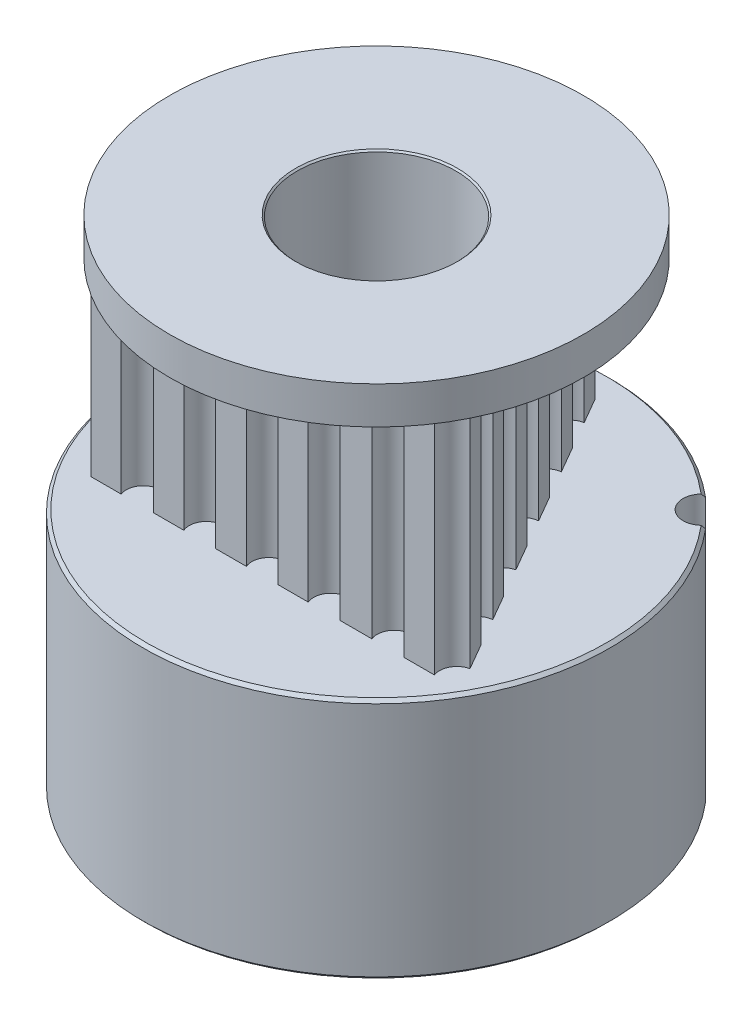
SolidWorks part; units mm, degrees
material "6061 slitina"
ref_plane "Přední rovina" through (0, 0, 0) normal (0, 0, 1) x (1, 0, 0)
ref_plane "Horní rovina" through (0, 0, 0) normal (0, 1, 0) x (1, 0, 0)
ref_plane "Pravá rovina" through (0, 0, 0) normal (1, 0, 0) x (0, 0, -1)
sketch "Skica1" plane through (0, 0, 0) normal (0, 1, 0) x (1, 0, 0)
  circle A0 centre (0, 0) radius 2.5
  arc B0 (-5.7301, 1.0983) -> (-5.3872, 2.2403) centre (-5.6803, 1.7058) ccw
  arc B1 (-5.7301, 1.0983) -> (-5.922, 1.0859) centre (-5.7841, 0.4401) ccw
  arc B2 (-5.922, 1.0859) -> (-6.0197, 1.0387) centre (-5.8743, 0.8624) ccw
  arc B3 (-6.0197, 1.0387) -> (-6.0791, 0.6004) centre (0, 0) ccw
  arc B4 (-6.0791, 0.6004) -> (-5.9974, 0.5289) centre (-5.892, 0.7317) ccw
  arc B5 (-5.9974, 0.5289) -> (-5.8158, 0.466) centre (-5.6927, 1.1148) ccw
  arc B6 (-5.7891, -0.7262) -> (-5.8158, 0.466) centre (-5.9294, -0.133) ccw
  arc B7 (-5.7891, -0.7262) -> (-5.9677, -0.7972) centre (-5.637, -1.3689) ccw
  arc B8 (-5.9677, -0.7972) -> (-6.0461, -0.8723) centre (-5.8532, -0.9951) ccw
  arc B9 (-6.0461, -0.8723) -> (-5.9671, -1.3075) centre (0, 0) ccw
  arc B10 (-5.9671, -1.3075) -> (-5.8673, -1.3503) centre (-5.8297, -1.1248) ccw
  arc B11 (-5.8673, -1.3503) -> (-5.6751, -1.354) centre (-5.7586, -0.6989) ccw
  arc B12 (-5.2813, -2.4796) -> (-5.6751, -1.354) centre (-5.5981, -1.9587) ccw
  arc B13 (-5.2813, -2.4796) -> (-5.4293, -2.6023) centre (-4.9381, -3.0438) ccw
  arc B14 (-5.4293, -2.6023) -> (-5.4806, -2.698) centre (-5.2593, -2.7551) ccw
  arc B15 (-5.4806, -2.698) -> (-5.271, -3.0875) centre (0, 0) ccw
  arc B16 (-5.271, -3.0875) -> (-5.1629, -3.0973) centre (-5.1968, -2.8713) ccw
  arc B17 (-5.1629, -3.0973) -> (-4.979, -3.0415) centre (-5.2608, -2.4442) ccw
  arc B18 (-4.2566, -3.9902) -> (-4.979, -3.0415) centre (-4.7188, -3.5928) ccw
  arc B19 (-4.2566, -3.9902) -> (-4.3594, -4.1527) centre (-3.7559, -4.4208) ccw
  arc B20 (-4.3594, -4.1527) -> (-4.3786, -4.2595) centre (-4.1505, -4.2455) ccw
  arc B21 (-4.3786, -4.2595) -> (-4.059, -4.5652) centre (0, 0) ccw
  arc B22 (-4.059, -4.5652) -> (-3.9531, -4.5412) centre (-4.0552, -4.3366) ccw
  arc B23 (-3.9531, -4.5412) -> (-3.7954, -4.4312) centre (-4.248, -3.9503) ccw
  arc B24 (-2.8152, -5.1103) -> (-3.7954, -4.4312) centre (-3.3776, -4.8751) ccw
  arc B25 (-2.8152, -5.1103) -> (-2.8628, -5.2965) centre (-2.2059, -5.3651) ccw
  arc B26 (-2.8628, -5.2965) -> (-2.8481, -5.4041) centre (-2.6354, -5.3203) ccw
  arc B27 (-2.8481, -5.4041) -> (-2.4496, -5.596) centre (0, 0) ccw
  arc B28 (-2.4496, -5.596) -> (-2.3563, -5.5405) centre (-2.5166, -5.3775) ccw
  arc B29 (-2.3563, -5.5405) -> (-2.2403, -5.3872) centre (-2.8194, -5.0696) ccw
  arc B30 (-1.0983, -5.7301) -> (-2.2403, -5.3872) centre (-1.7058, -5.6803) ccw
  arc B31 (-1.0983, -5.7301) -> (-1.0859, -5.922) centre (-0.4401, -5.7841) ccw
  arc B32 (-1.0859, -5.922) -> (-1.0387, -6.0197) centre (-0.8624, -5.8743) ccw
  arc B33 (-1.0387, -6.0197) -> (-0.6004, -6.0791) centre (0, 0) ccw
  arc B34 (-0.6004, -6.0791) -> (-0.5289, -5.9974) centre (-0.7317, -5.892) ccw
  arc B35 (-0.5289, -5.9974) -> (-0.466, -5.8158) centre (-1.1148, -5.6927) ccw
  arc B36 (0.7262, -5.7891) -> (-0.466, -5.8158) centre (0.133, -5.9294) ccw
  arc B37 (0.7262, -5.7891) -> (0.7972, -5.9677) centre (1.3689, -5.637) ccw
  arc B38 (0.7972, -5.9677) -> (0.8723, -6.0461) centre (0.9951, -5.8532) ccw
  arc B39 (0.8723, -6.0461) -> (1.3075, -5.9671) centre (0, 0) ccw
  arc B40 (1.3075, -5.9671) -> (1.3503, -5.8673) centre (1.1248, -5.8297) ccw
  arc B41 (1.3503, -5.8673) -> (1.354, -5.6751) centre (0.6989, -5.7586) ccw
  arc B42 (2.4796, -5.2813) -> (1.354, -5.6751) centre (1.9587, -5.5981) ccw
  arc B43 (2.4796, -5.2813) -> (2.6023, -5.4293) centre (3.0438, -4.9381) ccw
  arc B44 (2.6023, -5.4293) -> (2.698, -5.4806) centre (2.7551, -5.2593) ccw
  arc B45 (2.698, -5.4806) -> (3.0875, -5.271) centre (0, 0) ccw
  arc B46 (3.0875, -5.271) -> (3.0973, -5.1629) centre (2.8713, -5.1968) ccw
  arc B47 (3.0973, -5.1629) -> (3.0415, -4.979) centre (2.4442, -5.2608) ccw
  arc B48 (3.9902, -4.2566) -> (3.0415, -4.979) centre (3.5928, -4.7188) ccw
  arc B49 (3.9902, -4.2566) -> (4.1527, -4.3594) centre (4.4208, -3.7559) ccw
  arc B50 (4.1527, -4.3594) -> (4.2595, -4.3786) centre (4.2455, -4.1505) ccw
  arc B51 (4.2595, -4.3786) -> (4.5652, -4.059) centre (0, 0) ccw
  arc B52 (4.5652, -4.059) -> (4.5412, -3.9531) centre (4.3366, -4.0552) ccw
  arc B53 (4.5412, -3.9531) -> (4.4312, -3.7954) centre (3.9503, -4.248) ccw
  arc B54 (5.1103, -2.8152) -> (4.4312, -3.7954) centre (4.8751, -3.3776) ccw
  arc B55 (5.1103, -2.8152) -> (5.2965, -2.8628) centre (5.3651, -2.2059) ccw
  arc B56 (5.2965, -2.8628) -> (5.4041, -2.8481) centre (5.3203, -2.6354) ccw
  arc B57 (5.4041, -2.8481) -> (5.596, -2.4496) centre (0, 0) ccw
  arc B58 (5.596, -2.4496) -> (5.5405, -2.3563) centre (5.3775, -2.5166) ccw
  arc B59 (5.5405, -2.3563) -> (5.3872, -2.2403) centre (5.0696, -2.8194) ccw
  arc B60 (5.7301, -1.0983) -> (5.3872, -2.2403) centre (5.6803, -1.7058) ccw
  arc B61 (5.7301, -1.0983) -> (5.922, -1.0859) centre (5.7841, -0.4401) ccw
  arc B62 (5.922, -1.0859) -> (6.0197, -1.0387) centre (5.8743, -0.8624) ccw
  arc B63 (6.0197, -1.0387) -> (6.0791, -0.6004) centre (0, 0) ccw
  arc B64 (6.0791, -0.6004) -> (5.9974, -0.5289) centre (5.892, -0.7317) ccw
  arc B65 (5.9974, -0.5289) -> (5.8158, -0.466) centre (5.6927, -1.1148) ccw
  arc B66 (5.7891, 0.7262) -> (5.8158, -0.466) centre (5.9294, 0.133) ccw
  arc B67 (5.7891, 0.7262) -> (5.9677, 0.7972) centre (5.637, 1.3689) ccw
  arc B68 (5.9677, 0.7972) -> (6.0461, 0.8723) centre (5.8532, 0.9951) ccw
  arc B69 (6.0461, 0.8723) -> (5.9671, 1.3075) centre (0, 0) ccw
  arc B70 (5.9671, 1.3075) -> (5.8673, 1.3503) centre (5.8297, 1.1248) ccw
  arc B71 (5.8673, 1.3503) -> (5.6751, 1.354) centre (5.7586, 0.6989) ccw
  arc B72 (5.2813, 2.4796) -> (5.6751, 1.354) centre (5.5981, 1.9587) ccw
  arc B73 (5.2813, 2.4796) -> (5.4293, 2.6023) centre (4.9381, 3.0438) ccw
  arc B74 (5.4293, 2.6023) -> (5.4806, 2.698) centre (5.2593, 2.7551) ccw
  arc B75 (5.4806, 2.698) -> (5.271, 3.0875) centre (0, 0) ccw
  arc B76 (5.271, 3.0875) -> (5.1629, 3.0973) centre (5.1968, 2.8713) ccw
  arc B77 (5.1629, 3.0973) -> (4.979, 3.0415) centre (5.2608, 2.4442) ccw
  arc B78 (4.2566, 3.9902) -> (4.979, 3.0415) centre (4.7188, 3.5928) ccw
  arc B79 (4.2566, 3.9902) -> (4.3594, 4.1527) centre (3.7559, 4.4208) ccw
  arc B80 (4.3594, 4.1527) -> (4.3786, 4.2595) centre (4.1505, 4.2455) ccw
  arc B81 (4.3786, 4.2595) -> (4.059, 4.5652) centre (0, 0) ccw
  arc B82 (4.059, 4.5652) -> (3.9531, 4.5412) centre (4.0552, 4.3366) ccw
  arc B83 (3.9531, 4.5412) -> (3.7954, 4.4312) centre (4.248, 3.9503) ccw
  arc B84 (2.8152, 5.1103) -> (3.7954, 4.4312) centre (3.3776, 4.8751) ccw
  arc B85 (2.8152, 5.1103) -> (2.8628, 5.2965) centre (2.2059, 5.3651) ccw
  arc B86 (2.8628, 5.2965) -> (2.8481, 5.4041) centre (2.6354, 5.3203) ccw
  arc B87 (2.8481, 5.4041) -> (2.4496, 5.596) centre (0, 0) ccw
  arc B88 (2.4496, 5.596) -> (2.3563, 5.5405) centre (2.5166, 5.3775) ccw
  arc B89 (2.3563, 5.5405) -> (2.2403, 5.3872) centre (2.8194, 5.0696) ccw
  arc B90 (1.0983, 5.7301) -> (2.2403, 5.3872) centre (1.7058, 5.6803) ccw
  arc B91 (1.0983, 5.7301) -> (1.0859, 5.922) centre (0.4401, 5.7841) ccw
  arc B92 (1.0859, 5.922) -> (1.0387, 6.0197) centre (0.8624, 5.8743) ccw
  arc B93 (1.0387, 6.0197) -> (0.6004, 6.0791) centre (0, 0) ccw
  arc B94 (0.6004, 6.0791) -> (0.5289, 5.9974) centre (0.7317, 5.892) ccw
  arc B95 (0.5289, 5.9974) -> (0.466, 5.8158) centre (1.1148, 5.6927) ccw
  arc B96 (-0.7262, 5.7891) -> (0.466, 5.8158) centre (-0.133, 5.9294) ccw
  arc B97 (-0.7262, 5.7891) -> (-0.7972, 5.9677) centre (-1.3689, 5.637) ccw
  arc B98 (-0.7972, 5.9677) -> (-0.8723, 6.0461) centre (-0.9951, 5.8532) ccw
  arc B99 (-0.8723, 6.0461) -> (-1.3075, 5.9671) centre (0, 0) ccw
  arc B100 (-1.3075, 5.9671) -> (-1.3503, 5.8673) centre (-1.1248, 5.8297) ccw
  arc B101 (-1.3503, 5.8673) -> (-1.354, 5.6751) centre (-0.6989, 5.7586) ccw
  arc B102 (-2.4796, 5.2813) -> (-1.354, 5.6751) centre (-1.9587, 5.5981) ccw
  arc B103 (-2.4796, 5.2813) -> (-2.6023, 5.4293) centre (-3.0438, 4.9381) ccw
  arc B104 (-2.6023, 5.4293) -> (-2.698, 5.4806) centre (-2.7551, 5.2593) ccw
  arc B105 (-2.698, 5.4806) -> (-3.0875, 5.271) centre (0, 0) ccw
  arc B106 (-3.0875, 5.271) -> (-3.0973, 5.1629) centre (-2.8713, 5.1968) ccw
  arc B107 (-3.0973, 5.1629) -> (-3.0415, 4.979) centre (-2.4442, 5.2608) ccw
  arc B108 (-3.9902, 4.2566) -> (-3.0415, 4.979) centre (-3.5928, 4.7188) ccw
  arc B109 (-3.9902, 4.2566) -> (-4.1527, 4.3594) centre (-4.4208, 3.7559) ccw
  arc B110 (-4.1527, 4.3594) -> (-4.2595, 4.3786) centre (-4.2455, 4.1505) ccw
  arc B111 (-4.2595, 4.3786) -> (-4.5652, 4.059) centre (0, 0) ccw
  arc B112 (-4.5652, 4.059) -> (-4.5412, 3.9531) centre (-4.3366, 4.0552) ccw
  arc B113 (-4.5412, 3.9531) -> (-4.4312, 3.7954) centre (-3.9503, 4.248) ccw
  arc B114 (-5.1103, 2.8152) -> (-4.4312, 3.7954) centre (-4.8751, 3.3776) ccw
  arc B115 (-5.1103, 2.8152) -> (-5.2965, 2.8628) centre (-5.3651, 2.2059) ccw
  arc B116 (-5.2965, 2.8628) -> (-5.4041, 2.8481) centre (-5.3203, 2.6354) ccw
  arc B117 (-5.4041, 2.8481) -> (-5.596, 2.4496) centre (0, 0) ccw
  arc B118 (-5.596, 2.4496) -> (-5.5405, 2.3563) centre (-5.3775, 2.5166) ccw
  arc B119 (-5.5405, 2.3563) -> (-5.3872, 2.2403) centre (-5.0696, 2.8194) ccw
  dimension "D1" = 5
sketch_block_instance "Blok1-1"
sketch_block "Blok1"
extrude "Přidat vysunutím1" add sketch "Skica1" along normal blind 7 from offset 7.8
sketch "Skica2" plane through (0, 7.8, 0) normal (0, -1, 0) x (1, 0, 0)
  circle A0 centre (0, 0) radius 3.5
  circle A1 centre (0, 0) radius 2.5 construction
  circle A2 centre (0, 0) radius 2.5
  dimension "D1" = 7
extrude "Přidat vysunutím2" add sketch "Skica2" along normal blind 7.8
sketch "Skica3" plane through (0, 14.8, 0) normal (0, 1, 0) x (1, 0, 0)
  circle A0 centre (0, 0) radius 3.5
  circle A1 centre (0, 0) radius 2.5 construction
  circle A2 centre (0, 0) radius 2.5
  dimension "D1" = 7
extrude "Přidat vysunutím3" add sketch "Skica3" along normal blind 1.2
sketch "Skica5" plane through (0, 16, 0) normal (0, 1, 0) x (1, 0, 0)
  circle A0 centre (0, 0) radius 7.5
  circle A3 centre (0, 0) radius 3.5 construction
  circle A4 centre (0, 0) radius 3.5
  dimension "D1" = 15
extrude "Přidat vysunutím4" add sketch "Skica5" against normal up to surface (1.2 mm away) separate body up to face at (0, 14.8, 0)
sketch "Skica6" plane through (0, 0, 0) normal (0, -1, 0) x (1, 0, 0)
  circle A0 centre (0, 0) radius 7.5
  circle A1 centre (0, 0) radius 3.5 construction
  circle A2 centre (0, 0) radius 3.5
  circle A3 centre (0, 0) radius 7.5 construction
extrude "Přidat vysunutím5" add sketch "Skica6" against normal up to surface (7.8 mm away) separate body up to face at (0, 7.8, 0)
chamfer "Zkosení1" distance 0.1 angle 45 2 edges at (0, 14.8, 7.5) (0, 16, 7.5)
chamfer "Zkosení2" distance 0.1 angle 45 2 edges at (0, 0, -2.5) (0, 16, 2.5)
chamfer "Zkosení3" distance 0.1 angle 45 2 edges at (0, 0, -7.5) (0, 7.8, 7.5)
sketch "Sketch8" plane through (0, 16, 0) normal (0, 1, 0) x (1, 0, 0)
  circle A0 centre (0, 0) radius 6.65
extrude "Cut-Extrude2" cut sketch "Sketch8" against normal blind 5 flip side to cut contours A0
ref_plane "Plane1" through (0, 0, -7.5) normal (0, 0, -1) x (-1, 0, 0)
ref_plane "Plane2" through (-7.5, 0, 0) normal (-1, 0, 0) x (0, 0, 1)
sketch "Sketch20" plane through (-7.5, 0, 0) normal (-1, 0, 0) x (0, 0, 1)
  line L0 (0, 0.1) -> (0, 7.7)
  line L1 (-7.5, 0.1) -> (7.5, 0.1) construction
  line L2 (7.5, 7.7) -> (-7.5, 7.7) construction
  circle A0 centre (0, 3.9) radius 1.5
sketch "Sketch25" plane through (0, 7.8, 0) normal (0, 1, 0) x (1, 0, 0)
  line L0 (-0.7179, 6.0965) -> (-0.9071, 5.7689)
  line L5 (-5.5084, -3.67) -> (-4.5368, -3.67)
  line L6 (5.926, -2.9242) -> (5.4338, -2.0716)
  line L9 (-5.4363, -2.0759) -> (-5.8989, -2.8773)
  line L23 (-3.4987, -3.67) -> (-2.5208, -3.67)
  line L24 (-4.4422, -0.3541) -> (-4.912, -1.1678)
  line L26 (-1.4992, -3.67) -> (-0.513, -3.67)
  line L27 (2.4958, -3.67) -> (3.5189, -3.67)
  line L28 (4.926, -1.192) -> (4.4459, -0.3606)
  line L29 (4.549, -3.67) -> (5.5306, -3.67)
  line L30 (0.5086, -3.67) -> (1.4742, -3.67)
  line L31 (3.9112, 0.5657) -> (3.4185, 1.419)
  line L32 (1.9163, 4.0209) -> (1.4364, 4.8521)
  line L33 (-1.4233, 4.8748) -> (-1.9185, 4.0171)
  line L34 (2.9152, 2.2908) -> (2.4274, 3.1357)
  line L35 (0.9141, 5.7568) -> (0.4321, 6.5916)
  line L37 (-2.4409, 3.1122) -> (-2.9162, 2.2891)
  line L39 (-0.7179, 6.0965) -> (-0.4321, 6.5916)
  line L40 (-3.4352, 1.3901) -> (-3.9277, 0.5371)
  line L42 (-0.4321, 6.5916) -> (-0.9071, 5.7689) [skipped]
  arc A24 (-0.4321, 6.5916) -> (0.4321, 6.5916) centre (0, 6.94) ccw
  arc A25 (-1.4233, 4.8748) -> (-0.9071, 5.7689) centre (-0.9887, 5.22) ccw
  arc A26 (-2.4409, 3.1122) -> (-1.9185, 4.0171) centre (-2.0176, 3.471) ccw
  arc A27 (0.9141, 5.7568) -> (1.4364, 4.8521) centre (1.0128, 5.2106) ccw
  arc A28 (1.9163, 4.0209) -> (2.4274, 3.1357) centre (1.9844, 3.4701) ccw
  arc A29 (-3.4352, 1.3901) -> (-2.9162, 2.2891) centre (-3.0054, 1.7413) ccw
  arc A30 (-4.4422, -0.3541) -> (-3.9277, 0.5371) centre (-4.0048, -0.0125) ccw
  arc A31 (-5.4363, -2.0759) -> (-4.912, -1.1678) centre (-5.0165, -1.7129) ccw
  arc A32 (-5.5084, -3.67) -> (-5.8989, -2.8773) centre (-6.0049, -3.4221) ccw
  arc A33 (-3.4987, -3.67) -> (-4.5368, -3.67) centre (-4.0177, -3.4735) ccw
  arc A34 (-1.4992, -3.67) -> (-2.5208, -3.67) centre (-2.01, -3.4529) ccw
  arc A35 (0.5086, -3.67) -> (-0.513, -3.67) centre (-0.0022, -3.4529) ccw
  arc A36 (2.4958, -3.67) -> (1.4742, -3.67) centre (1.985, -3.4529) ccw
  arc A37 (4.549, -3.67) -> (3.5189, -3.67) centre (4.0339, -3.4632) ccw
  arc A38 (2.9152, 2.2908) -> (3.4185, 1.419) centre (2.9643, 1.738) ccw
  arc A39 (3.9112, 0.5657) -> (4.4459, -0.3606) centre (4.05, 0.0283) ccw
  arc A40 (4.926, -1.192) -> (5.4338, -2.0716) centre (4.9859, -1.7438) ccw
  arc A41 (5.926, -2.9242) -> (5.5306, -3.67) centre (6.0467, -3.4659) ccw
  point P0 (-1.0017, 5.205)
  point P6 (-2.0034, 3.47)
  point P7 (-3.0051, 1.735)
  point P8 (0, 0)
  point P9 (-4.0068, 0)
  point P10 (-5.0085, -1.735)
  point P11 (5.0085, -1.735)
  point P12 (4.0068, 0)
  point P13 (3.0051, 1.735)
  point P14 (2.0034, 3.47)
  point P15 (1.0017, 5.205)
  point P16 (-4.0068, -3.47)
  point P20 (-2.0034, -3.47)
  point P21 (0, -3.47)
  point P23 (2.0034, -3.47)
  point P24 (4.0068, -3.47)
sketch "Sketch30" plane through (0, 0, 0) normal (0, -1, 0) x (1, 0, 0)
  line L0 (0, 0) -> (6.782, 0)
  line L1 (6.782, 0) -> (0, -6.782)
  line L2 (-0.1186, 0) -> (3.391, -3.391)
  line L3 (3.391, -3.391) -> (4.7956, -4.7956)
  line L4 (4.7956, -4.7956) -> (5.2326, -5.2326)
  circle A0 centre (0, 0) radius 6.782
  circle A1 centre (0, 0) radius 7.4 construction
  circle A2 centre (5.2326, -5.2326) radius 0.618
sketch "Sketch31" plane through (0, 0, 0) normal (0, -1, 0) x (1, 0, 0)
  circle A1 centre (0, 0) radius 2.55
sketch "Sketch19" plane through (0, 0, -7.5) normal (0, 0, -1) x (-1, 0, 0)
  line L0 (0, 0.1) -> (0, 7.7)
  line L1 (7.5, 0.1) -> (-7.5, 0.1) construction
  line L2 (-7.5, 7.7) -> (7.5, 7.7) construction
  circle A0 centre (0, 3.9) radius 1.5
sketch "Sketch32" plane through (0, 7.8, 0) normal (0, 1, 0) x (1, 0, 0)
  circle A0 centre (0, 0) radius 6.65
extrude "Cut-Extrude3" cut sketch "Sketch32" along normal blind 7
extrude "Boss-Extrude1" add sketch "Sketch25" along normal blind 7
sketch "Sketch34" plane through (0, 16, 0) normal (0, 1, 0) x (1, 0, 0)
  circle A0 centre (0, 0) radius 2.55
extrude "Cut-Extrude4" cut sketch "Sketch34" against normal blind 30
extrude "Cut-Extrude5" cut sketch "Sketch20" against normal blind 8 contours A0
extrude "Cut-Extrude6" cut sketch "Sketch19" against normal blind 8 contours A0
extrude "Cut-Extrude7" cut sketch "Sketch30" against normal blind 8 contours A2
